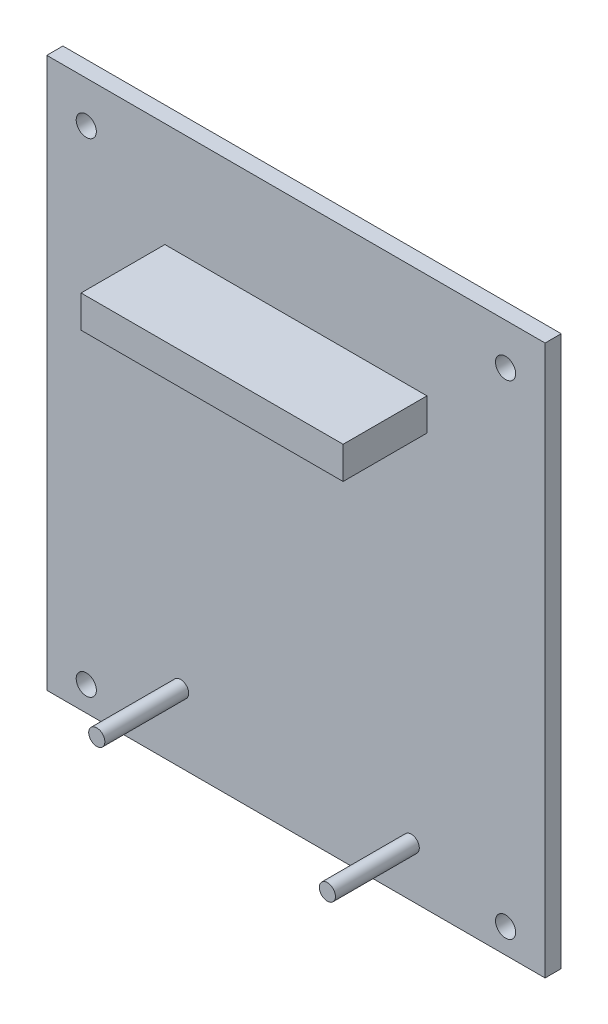
SolidWorks part; units mm, degrees
ref_plane "Front Plane" through (0, 0, 0) normal (0, 0, 1) x (1, 0, 0)
ref_plane "Top Plane" through (0, 0, 0) normal (0, 1, 0) x (1, 0, 0)
ref_plane "Right Plane" through (0, 0, 0) normal (1, 0, 0) x (0, 0, -1)
sketch "Sketch1" plane through (0, 0, 0) normal (0, 0, 1) x (1, 0, 0)
  line L0 (6.223, 80.1116) -> (72.263, 80.1116) construction
  line L1 (0, 86.614) -> (78.486, 86.614)
  line L2 (0, 86.614) -> (0, 0)
  line L3 (0, 0) -> (78.486, 0)
  line L4 (78.486, 86.614) -> (78.486, 0)
  line L5 (72.263, 80.1116) -> (72.263, 3.9116) construction
  line L6 (72.263, 3.9116) -> (6.223, 3.9116) construction
  line L7 (6.223, 3.9116) -> (6.223, 80.1116) construction
  line L8 (39.243, 86.614) -> (39.243, 0) construction
  line L9 (6.223, 42.0116) -> (72.263, 42.0116) construction
  circle A0 centre (6.223, 80.1116) radius 1.5875
  circle A1 centre (72.263, 80.1116) radius 1.5875
  circle A2 centre (72.263, 3.9116) radius 1.5875
  circle A3 centre (6.223, 3.9116) radius 1.5875
  point P18 (39.243, 42.0116)
  point P22 (39.243, 43.307)
  dimension "D3" = 3.175
  dimension "D1" = 76.2
  dimension "D2" = 66.04
  dimension "D4" = 78.486
  dimension "D5" = 86.614
  dimension "D6" = 2.5908
extrude "Boss-Extrude1" add sketch "Sketch1" along normal blind 2.54
sketch "Sketch2" plane through (0, 0, 2.54) normal (0, 0, 1) x (1, 0, 0)
  line L0 (39.243, 86.614) -> (39.243, 70.104) construction
  line L1 (18.6055, 70.104) -> (59.8805, 70.104)
  line L2 (18.6055, 70.104) -> (18.6055, 65.024)
  line L3 (18.6055, 65.024) -> (59.8805, 65.024)
  line L4 (59.8805, 70.104) -> (59.8805, 65.024)
  line L5 (78.486, 86.614) -> (0, 86.614) construction
  line L6 (21.082, 10.7569) -> (57.404, 10.7569) construction
  line L7 (39.243, 10.7569) -> (39.243, 0) construction
  line L8 (0, 0) -> (78.486, 0) construction
  line L9 (57.404, 10.7569) -> (57.404, 7.8105) construction
  circle A0 centre (21.082, 10.7569) radius 1.27
  circle A2 centre (57.404, 7.8105) radius 1.27
  point P10 (62.2732, -1.3207)
  dimension "D6" = 2.54
  dimension "D1" = 5.08
  dimension "D2" = 41.275
  dimension "D3" = 16.51
  dimension "D4" = 10.7569
  dimension "D5" = 36.322
  dimension "D7" = 2.9464
extrude "Boss-Extrude2" add sketch "Sketch2" along normal blind 13.208
sketch "Sketch3" plane through (0, 0, 2.54) normal (0, 0, 1) x (1, 0, 0)
  line L0 (57.404, 7.8105) -> (57.404, 3.9116) construction
  line L1 (57.404, 3.9116) -> (72.263, 3.9116) construction
  line L2 (0, 0) -> (78.486, 0) construction
  circle A0 centre (72.263, 3.9116) radius 1.5875 construction
  point P9 (0, 0)
  dimension "D1" = 14.859
  dimension "D2" = 3.8989
